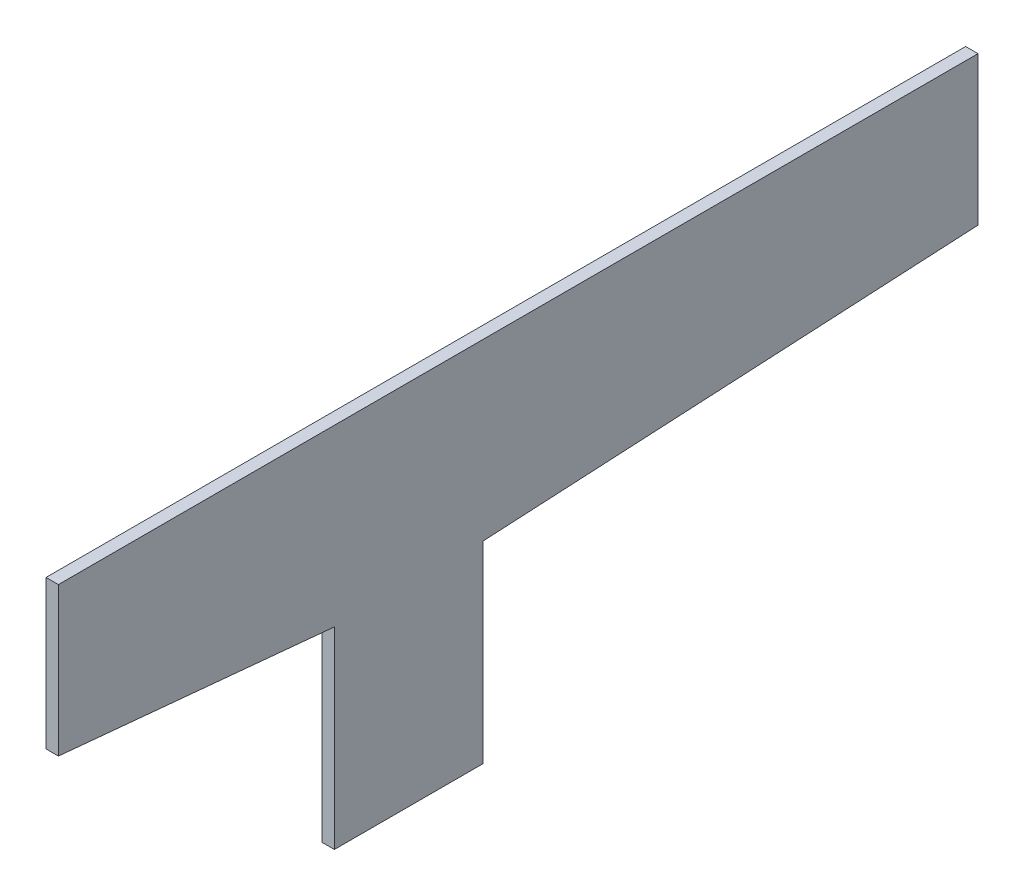
SolidWorks part; units mm, degrees
ref_plane "Front Plane" through (0, 0, 0) normal (0, 0, 1) x (1, 0, 0)
ref_plane "Top Plane" through (0, 0, 0) normal (0, 1, 0) x (1, 0, 0)
ref_plane "Right Plane" through (0, 0, 0) normal (1, 0, 0) x (0, 0, -1)
sketch "Sketch2" plane through (0, 0, 0) normal (1, 0, 0) x (0, 0, -1)
  line L0 (-19.05, 11.35) -> (-19.05, -38.1)
  line L1 (-19.05, -38.1) -> (19.05, -38.1)
  line L2 (19.05, -38.1) -> (19.05, 11.35)
  line L3 (19.05, 11.35) -> (146.05, 18.05)
  line L4 (146.05, 18.05) -> (146.05, 56.15)
  line L5 (146.05, 56.15) -> (-89.85, 56.15)
  line L6 (-89.85, 56.15) -> (-89.85, 18.05)
  line L7 (-89.85, 18.05) -> (-19.05, 11.35)
  line L8 (140.5032, 8.175) -> (130.2734, 8.175) construction
  line L9 (140.5032, 8.175) -> (130.2734, 8.175) construction
  line L10 (214.95, 56.15) -> (-89.85, 56.15) construction
  line L11 (214.95, 56.15) -> (-89.85, 56.15) construction
  point P10 (0, -38.1)
  dimension "D1" = 38.1
  dimension "D2" = 38.1
  dimension "D3" = 3.175
  dimension "D4" = 38.1
  dimension "D5" = 127
extrude "Boss-Extrude1" add sketch "Sketch2" along normal mid plane 3.175
